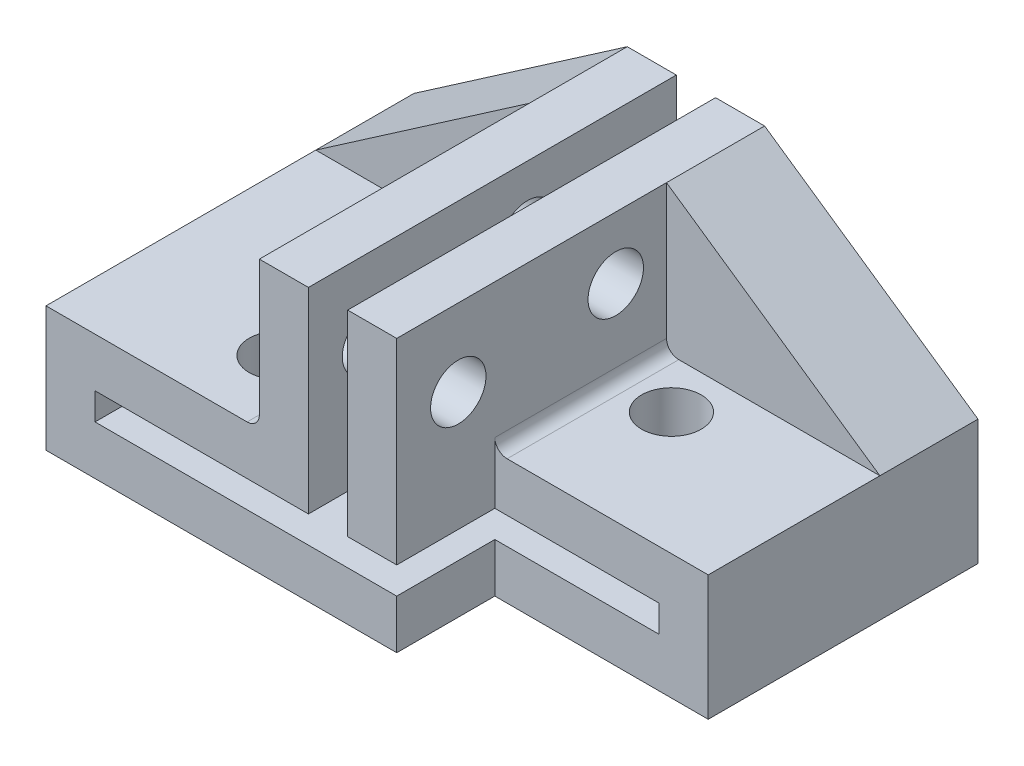
SolidWorks part; units mm, degrees
ref_plane "Front Plane" through (0, 0, 0) normal (0, 0, 1) x (1, 0, 0)
ref_plane "Top Plane" through (0, 0, 0) normal (0, 1, 0) x (1, 0, 0)
ref_plane "Right Plane" through (0, 0, 0) normal (1, 0, 0) x (0, 0, -1)
sketch "Sketch1" plane through (0, 0, 0) normal (0, 0, 1) x (1, 0, 0)
  line L0 (0, 0) -> (0, -6)
  line L1 (0, -6) -> (-8.7, -6)
  line L2 (-8.7, -6) -> (-8.7, -11.1)
  line L3 (-8.7, -11.1) -> (14.3, -11.1)
  line L4 (14.3, -11.1) -> (14.3, -6)
  line L5 (14.3, -6) -> (5.6, -6)
  line L6 (5.6, -6) -> (5.6, 0)
  line L7 (5.6, 0) -> (3.6, 0)
  line L8 (2, -8) -> (-6.7, -8)
  line L9 (-6.7, -8) -> (-6.7, -9.1)
  line L10 (-6.7, -9.1) -> (12.3, -9.1)
  line L11 (12.3, -9.1) -> (12.3, -8)
  line L12 (12.3, -8) -> (3.6, -8)
  line L13 (3.6, -8) -> (3.6, -3.5411)
  line L14 (3.6, -3.5411) -> (3.6, 0)
  line L15 (2, -8) -> (2, 0)
  line L16 (2, 0) -> (0, 0)
  line L17 (2.8, -11.1) -> (2.8, 0.7818) construction
  dimension "D1" = 1.1
  dimension "D2" = 2
  dimension "D3" = 2
  dimension "D4" = 2
  dimension "D5" = 19
  dimension "D6" = 1.6
  dimension "D7" = 2
  dimension "D8" = 2
  dimension "D9" = 2
  dimension "D10" = 8
extrude "Boss-Extrude1" add sketch "Sketch1" along normal blind 15 contours L0 L1 L2 L3 L4 L5 L6 L7 L14 L13 L12 L11 L10 L9 L8 L15 L16
sketch "Sketch2" plane through (0, -6, 0) normal (0, 1, 0) x (1, 0, 0)
  line L0 (14.3, -11) -> (5.6, -11)
  line L1 (14.3, -15) -> (14.3, 0) construction
  line L2 (5.6, -11) -> (5.6, -15)
  line L3 (14.3, -15) -> (5.6, -15) construction
  line L4 (5.6, -15) -> (14.3, -15)
  line L5 (14.3, -15) -> (14.3, -11)
  line L6 (5.6, -15) -> (5.6, 0) construction
  dimension "D1" = 4
extrude "Cut-Extrude1" cut sketch "Sketch2" against normal blind 15 contours L4 L5 L0 L2
sketch "Sketch4" plane through (0, 0, 0) normal (-1, 0, 0) x (0, 0, 1)
  line L0 (2.2954, -2.1666) -> (15.0384, -3.3936) construction
  line L2 (15, 0) -> (0, 0) construction
  line L3 (15, 0) -> (15, -6) construction
  circle A0 centre (12.49, -3.1482) radius 1.1303
  circle A2 centre (6.0697, -2.53) radius 1.1303
  dimension "D1" = 2.2606
  dimension "D2" = 6.45
  dimension "D4" = 5.5
  dimension "D5" = 2.53
  dimension "D6" = 2.51
other "AlignGroup1"
other "AlignGroup2"
extrude "Cut-Extrude2" cut sketch "Sketch4" against normal blind 15
sketch "Sketch5" plane through (0, -6, 0) normal (0, 1, 0) x (1, 0, 0)
  line L1 (-2.2, -6) -> (-7.8286, -6) construction
  line L4 (-8.7, -15) -> (-8.7, 0) construction
  line L6 (-6.7, -15) -> (5.6, -15) construction
  line L7 (14.3, -11) -> (14.3, 0) construction
  circle A0 centre (-2.2, -6) radius 1.215
  circle A1 centre (7.8, -6) radius 1.215
  circle A3 centre (-2.2, -12) radius 1.215
  dimension "D2" = 2.43
  dimension "D1" = 3
  dimension "D3" = 6
  dimension "D4" = 6.5
  dimension "D5" = 6.5
extrude "Cut-Extrude3" cut sketch "Sketch5" against normal blind 15 contours A3 | A1 | A0
ref_plane "Plane1" through (0, 0, 2) normal (0, 0, -1) x (-1, 0, 0)
sketch "Sketch6" plane through (0, 0, 2) normal (0, 0, -1) x (-1, 0, 0)
  line L0 (0, -6) -> (8.7, -6) construction
  line L1 (0, 0) -> (0, -6) construction
  line L2 (0, -6) -> (8.7, -6)
  line L3 (0, 0) -> (0, -6)
  line L4 (0, 0) -> (8.7, -6)
extrude "Boss-Extrude2" add sketch "Sketch6" along normal blind 2 and the other way blind 2
ref_plane "Plane2" through (2.8, 0, 0) normal (1, 0, 0) x (0, 0, -1)
mirror "Mirror1" about plane through (2.8, 0, 0) normal (1, 0, 0) of "Boss-Extrude2"
fillet "Fillet2" radius 0.5 2 edges at (5.6, -6, 7.5) (0, -6, 9.5)
